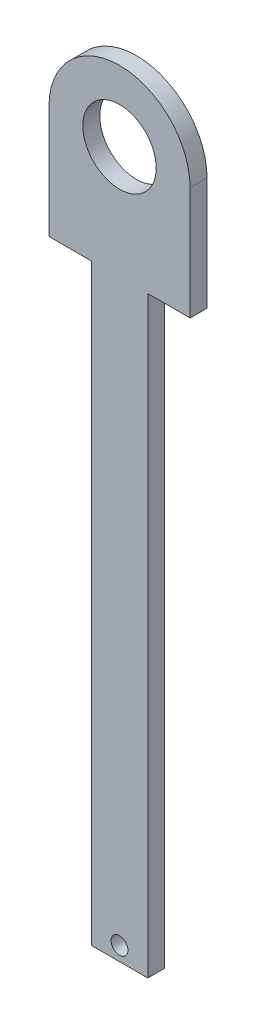
SolidWorks part; units mm, degrees
material "AISI 1030 HR"
ref_plane "Front Plane" through (0, 0, 0) normal (0, 0, 1) x (1, 0, 0)
ref_plane "Top Plane" through (0, 0, 0) normal (0, 1, 0) x (1, 0, 0)
ref_plane "Right Plane" through (0, 0, 0) normal (1, 0, 0) x (0, 0, -1)
sketch "Sketch1" plane through (0, 0, 0) normal (0, 0, 1) x (1, 0, 0)
  line L0 (150.5494, 27.7147) -> (150.1004, 27.7564)
  line L2 (77.4581, 42.6185) -> (77.4581, 2.6185)
  line L5 (27.4581, 42.6185) -> (27.4581, 2.6185)
  line L6 (27.4581, 2.6185) -> (77.4581, 2.6185)
  line L7 (77.4581, 42.6185) -> (77.4581, 2.6185)
  circle A0 centre (52.4581, 42.6185) radius 13
  arc A1 (77.4581, 42.6185) -> (27.4581, 42.6185) centre (52.4581, 42.6185) ccw
  dimension "D1" = 26
  dimension "D2" = 50
  dimension "D3" = 40
  dimension "D4" = 50
extrude "Boss-Extrude3" add sketch "Sketch1" along normal blind 6 contours L2 A1 L5 L6 A0
sketch "Sketch3" plane through (0, 2.6185, 0) normal (0, -1, 0) x (1, 0, 0)
  line L0 (27.4581, 3) -> (77.4581, 3) construction
  line L1 (27.4581, 6) -> (27.4581, 0) construction
  line L2 (77.4581, 6) -> (77.4581, 0) construction
  line L3 (52.4581, 6) -> (52.4581, 0) construction
  line L4 (27.4581, 6) -> (77.4581, 6) construction
  line L5 (27.4581, 0) -> (77.4581, 0) construction
  line L7 (62.4581, 0) -> (42.4581, 0)
  line L8 (62.4581, 0) -> (62.4581, 6)
  line L9 (62.4581, 6) -> (42.4581, 6)
  line L10 (42.4581, 0) -> (42.4581, 6)
  line L11 (62.4581, 0) -> (42.4581, 6) construction
  line L12 (62.4581, 6) -> (42.4581, 0) construction
  point P12 (52.4581, 3)
  dimension "D1" = 6
  dimension "D2" = 20
extrude "Boss-Extrude4" add sketch "Sketch3" along normal blind 200
sketch "Sketch5" plane through (0, 0, 6) normal (0, 0, 1) x (1, 0, 0)
  line L0 (52.4581, -197.3815) -> (52.4581, -207.3815) construction
  line L1 (62.4581, -197.3815) -> (42.4581, -197.3815) construction
  line L3 (42.4581, -207.3815) -> (62.4581, -207.3815)
  line L4 (42.4581, -207.3815) -> (42.4581, -197.3815)
  line L5 (42.4581, -197.3815) -> (62.4581, -197.3815)
  line L6 (62.4581, -207.3815) -> (62.4581, -197.3815)
  line L7 (42.4581, -207.3815) -> (62.4581, -197.3815) construction
  line L8 (42.4581, -197.3815) -> (62.4581, -207.3815) construction
  circle A0 centre (52.4581, -202.3815) radius 3
  point P5 (52.4581, -202.3815)
  dimension "D3" = 6
  dimension "D1" = 10
  dimension "D2" = 20
extrude "Boss-Extrude5" add sketch "Sketch5" against normal blind 6
